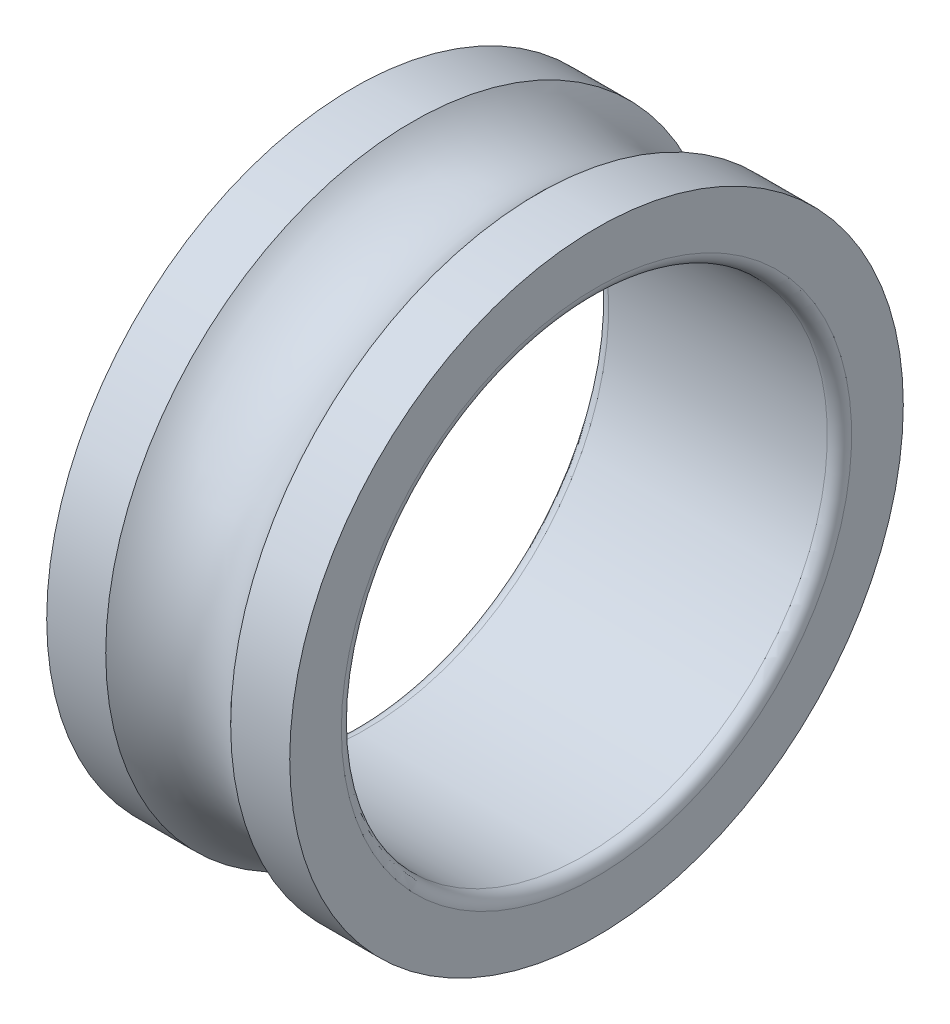
SolidWorks part; units mm, degrees
ref_plane "Plane1" through (0, 0, 0) normal (0, 0, 1) x (1, 0, 0)
ref_plane "Plane2" through (0, 0, 0) normal (0, 1, 0) x (1, 0, 0)
ref_plane "Plane3" through (0, 0, 0) normal (1, 0, 0) x (0, 0, -1)
sketch "Esquisse1" plane through (0, 0, 0) normal (0, 0, 1) x (1, 0, 0)
  line L0 (0, 5.05) -> (0, 4.2) construction
  line L1 (0, 5.05) -> (0.9717, 5.05) construction
  line L2 (3.0283, 5.05) -> (4, 5.05) construction
  line L3 (4, 4.2) -> (4, 5.05) construction
  line L4 (3.8, 4) -> (0.2, 4) construction
  line L5 (0, 5.05) -> (0, 4.2)
  line L6 (0, 5.05) -> (0.9717, 5.05)
  line L7 (3.0283, 5.05) -> (4, 5.05)
  line L8 (4, 4.2) -> (4, 5.05)
  line L9 (3.8, 4) -> (0.2, 4)
  line L10 (0, 0) -> (21.7661, 0) construction
  line L11 (0, 0) -> (37.6531, 0) construction
  arc A0 (0, 4.2) -> (0.2, 4) centre (0.2, 4.2) ccw construction
  circle A1 centre (2, 6) radius 1.4 construction
  arc A2 (3.8, 4) -> (4, 4.2) centre (3.8, 4.2) ccw construction
  arc A3 (0, 4.2) -> (0.2, 4) centre (0.2, 4.2) ccw
  arc A4 (0.9717, 5.05) -> (3.0283, 5.05) centre (2, 6) ccw
  arc A5 (3.8, 4) -> (4, 4.2) centre (3.8, 4.2) ccw
revolve "Base-Révolution" add sketch "Esquisse1" angle 360 about L10
